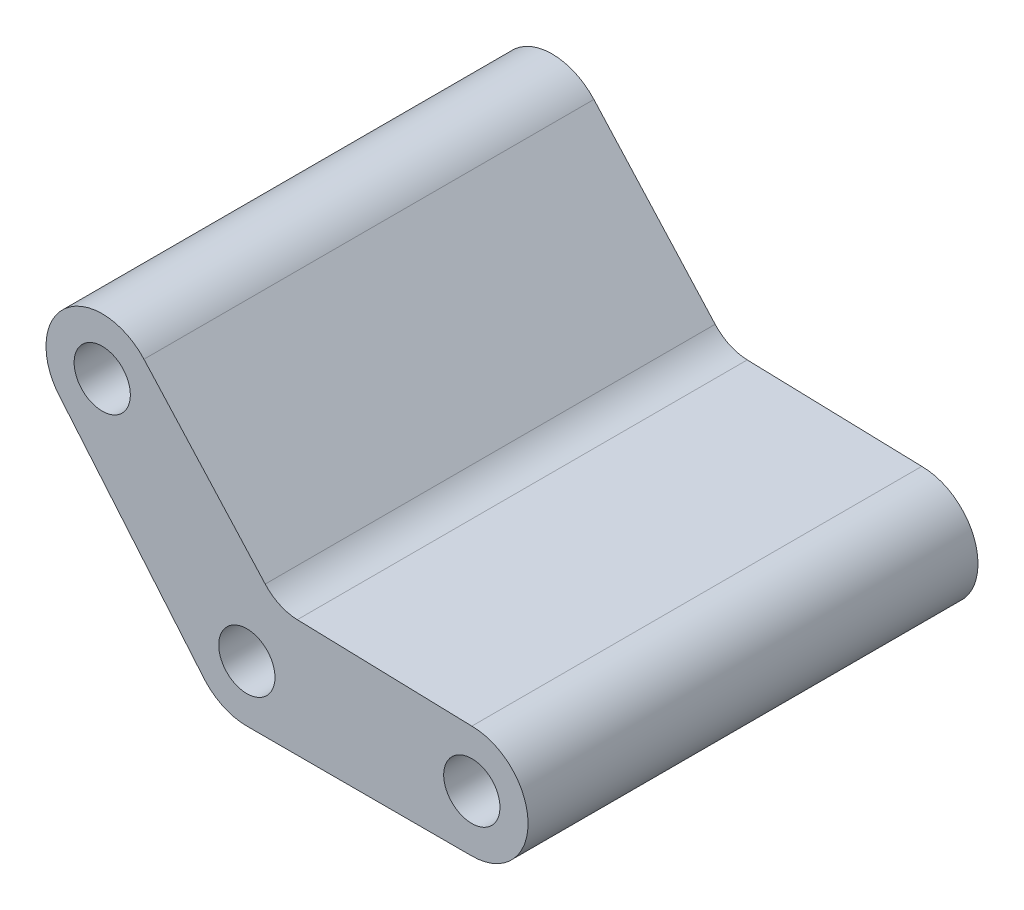
SolidWorks part; units mm, degrees
ref_plane "Front Plane" through (0, 0, 0) normal (0, 0, 1) x (1, 0, 0)
ref_plane "Top Plane" through (0, 0, 0) normal (0, 1, 0) x (1, 0, 0)
ref_plane "Right Plane" through (0, 0, 0) normal (1, 0, 0) x (0, 0, -1)
sketch "Sketch2" plane through (0, 0, 0) normal (0, 0, 1) x (1, 0, 0)
  line L0 (-304.5455, 0) -> (304.5455, 0) construction
  line L1 (0, 185) -> (0, -205.9091) construction
  line L2 (0, 0) -> (200, 0) construction
  line L3 (44.858, 54.3767) -> (200, 50)
  line L4 (0, -50) -> (200, -50)
  line L5 (0, 0) -> (-128.5575, 153.2089) construction
  line L6 (-37.0876, -33.5337) -> (-165.6451, 119.6752)
  line L7 (16.3159, 67.5338) -> (-91.4699, 186.7426)
  arc A0 (-37.0876, -33.5337) -> (0, -50) centre (0, 0) ccw
  arc A1 (200, -50) -> (200, 50) centre (200, 0) ccw
  arc A2 (-37.0876, -33.5337) -> (0, -50) centre (0, 0) ccw
  arc A3 (-91.4699, 186.7426) -> (-165.6451, 119.6752) centre (-128.5575, 153.2089) ccw
  circle A4 centre (-128.5575, 153.2089) radius 25
  circle A5 centre (0, 0) radius 25
  circle A6 centre (200, 0) radius 25
  arc A7 (16.3159, 67.5338) -> (44.858, 54.3767) centre (45.986, 94.3608) ccw
  point P7 (100, 0)
  point P12 (-67.0675, 74.1752)
  point P25 (0, 0)
  point P26 (0, 0)
  point P27 (0, 0)
  dimension "D3" = 50
  dimension "D4" = 50
  dimension "D5" = 50
  dimension "D6" = 40
  dimension "D1" = 200
  dimension "D2" = 200
  dimension "D8" = 130
extrude "Boss-Extrude1" add sketch "Sketch2" along normal blind 400 contours A7 L7 A3 L6 A0 L4 A1 L3 A6 A5 A4
